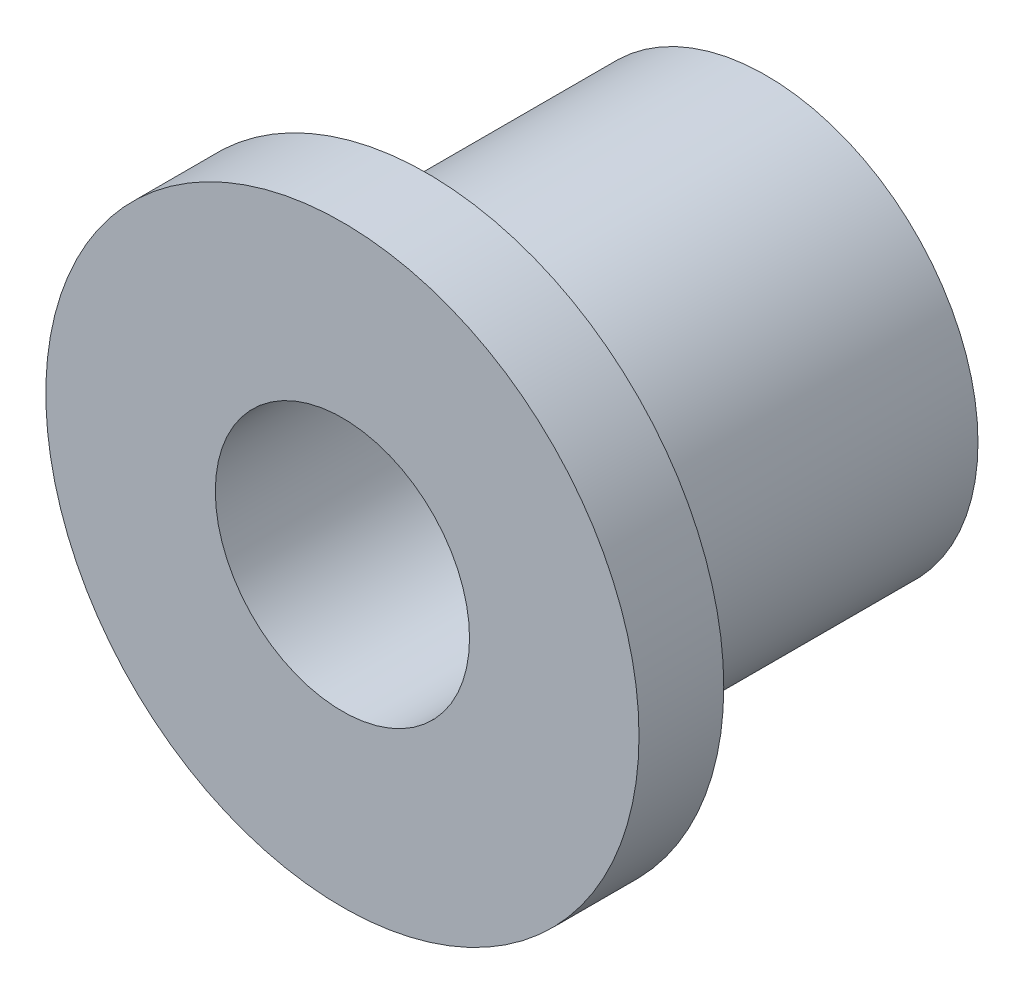
SolidWorks part; units mm, degrees
material "PTFE (general)"
ref_plane "Front Plane" through (0, 0, 0) normal (0, 0, 1) x (1, 0, 0)
ref_plane "Top Plane" through (0, 0, 0) normal (0, 1, 0) x (1, 0, 0)
ref_plane "Right Plane" through (0, 0, 0) normal (1, 0, 0) x (0, 0, -1)
sketch "Sketch1" plane through (0, 0, 0) normal (0, 0, 1) x (1, 0, 0)
  circle A0 centre (0, 0) radius 3.9688
  circle A1 centre (0, 0) radius 2.3812
  dimension "D1" = 4.7625
  dimension "D2" = 7.9375
extrude "Boss-Extrude1" add sketch "Sketch1" along normal blind 6.35
sketch "Sketch2" plane through (0, 0, 6.35) normal (0, 0, 1) x (1, 0, 0)
  circle A0 centre (0, 0) radius 5.5562
  circle A1 centre (0, 0) radius 2.3812 construction
  circle A2 centre (0, 0) radius 2.3812
  dimension "D1" = 11.1125
extrude "Boss-Extrude2" add sketch "Sketch2" along normal blind 1.5875
